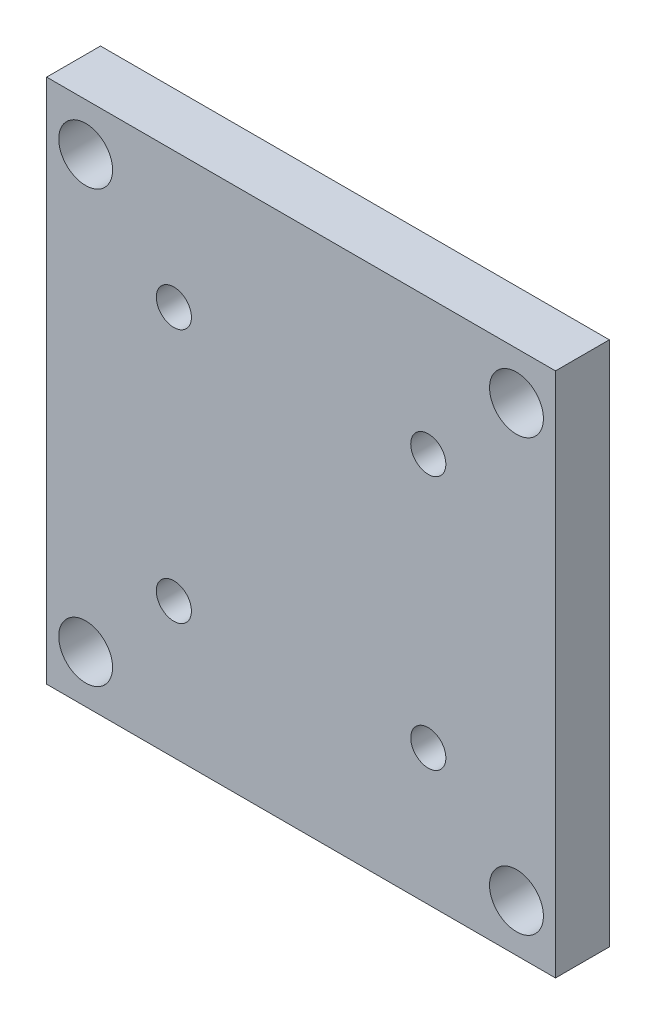
SolidWorks part; units mm, degrees
ref_plane "Front Plane" through (0, 0, 0) normal (0, 0, 1) x (1, 0, 0)
ref_plane "Top Plane" through (0, 0, 0) normal (0, 1, 0) x (1, 0, 0)
ref_plane "Right Plane" through (0, 0, 0) normal (1, 0, 0) x (0, 0, -1)
sketch "Sketch1" plane through (0, 0, 0) normal (0, 0, 1) x (1, 0, 0)
  line L0 (25.4, 38.5091) -> (25.4, -45.4774) construction
  line L1 (-30, -31) -> (30, -31)
  line L2 (-30, -31) -> (-30, 31)
  line L3 (-30, 31) -> (30, 31)
  line L4 (30, -31) -> (30, 31)
  line L5 (-30, -31) -> (30, 31) construction
  line L6 (-30, 31) -> (30, -31) construction
  line L7 (-20.5986, 25.4) -> (33.8212, 25.4) construction
  line L8 (0, 35.5444) -> (0, -29.0334) construction
  line L9 (-26.8976, 0) -> (23.1056, 0) construction
  line L10 (-25.4, 25.4) -> (-20.5986, 25.4) construction
  circle A1 centre (25.4, 25.4) radius 3.175
  circle A2 centre (-25.4, 25.4) radius 3.175
  circle A3 centre (25.4, -25.4) radius 3.175
  circle A4 centre (-25.4, -25.4) radius 3.175
  circle A5 centre (-15, 15) radius 2.071
  circle A6 centre (-15, -15) radius 2.071
  circle A7 centre (15, -15) radius 2.071
  circle A8 centre (15, 15) radius 2.071
  point P0 (0, 0)
  dimension "D6" = 15
  dimension "D8" = 6.35
  dimension "D9" = 4.142
  dimension "D1" = 60
  dimension "D2" = 62
  dimension "D4" = 25.4
  dimension "D5" = 25.4
  dimension "D7" = 15
extrude "Boss-Extrude1" add sketch "Sketch1" along normal blind 6.35
